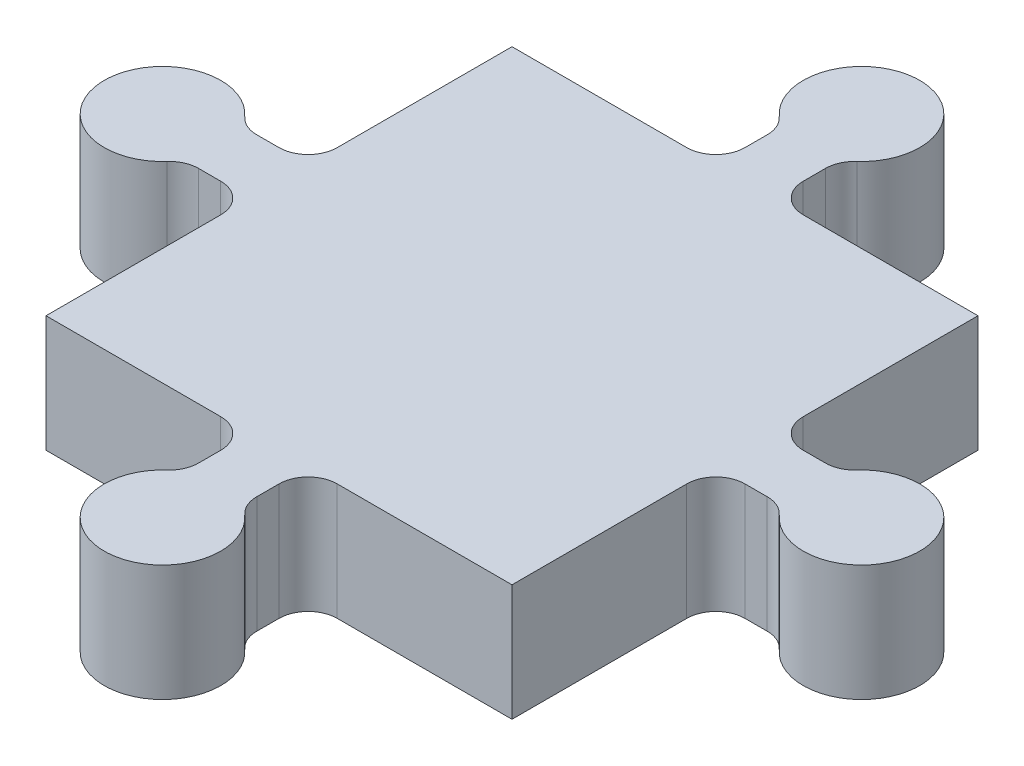
SolidWorks part; units mm, degrees
ref_plane "Front Plane" through (0, 0, 0) normal (0, 0, 1) x (1, 0, 0)
ref_plane "Top Plane" through (0, 0, 0) normal (0, 1, 0) x (1, 0, 0)
ref_plane "Right Plane" through (0, 0, 0) normal (1, 0, 0) x (0, 0, -1)
sketch "Sketch1" plane through (0, 0, 0) normal (0, 1, 0) x (1, 0, 0)
  line L0 (-4, 4) -> (4, -4) construction
  line L1 (-4, 4) -> (4, 4)
  line L2 (-4, 4) -> (-4, -4)
  line L3 (-4, -4) -> (4, -4)
  line L4 (4, 4) -> (4, -4)
  line L5 (-4, -4) -> (4, 4) construction
  line L6 (0, 6) -> (0, 4)
  line L7 (4, 0.5) -> (6, 0.5)
  line L8 (-0.5, 4) -> (0.5, 4)
  line L9 (-0.5, 4) -> (-0.5, 6)
  line L10 (-0.5, 6) -> (0.5, 6)
  line L11 (0.5, 4) -> (0.5, 6)
  line L12 (4, 0.5) -> (4, -0.5)
  line L13 (4, -0.5) -> (6, -0.5)
  line L14 (6, 0.5) -> (6, -0.5)
  line L15 (0.5, -4) -> (0.5, -6)
  line L16 (0.5, -4) -> (-0.5, -4)
  line L17 (-0.5, -4) -> (-0.5, -6)
  line L18 (0.5, -6) -> (-0.5, -6)
  line L19 (-4, -0.5) -> (-6, -0.5)
  line L20 (-4, -0.5) -> (-4, 0.5)
  line L21 (-4, 0.5) -> (-6, 0.5)
  line L22 (-6, -0.5) -> (-6, 0.5)
  circle A0 centre (0, 6) radius 1
  circle A1 centre (6, 0) radius 1
  circle A2 centre (0, -6) radius 1
  circle A3 centre (-6, 0) radius 1
  point P4 (0, 0)
  point P14 (0, 6)
  point P35 (0, 0)
  dimension "D3" = 2
  dimension "D1" = 8
  dimension "D2" = 8
  dimension "D4" = 2
  dimension "D5" = 1
  dimension "D6" = 4
extrude "Boss-Extrude1" add sketch "Sketch1" along normal blind 2 contours L4 L1 L2 L3 | L21 A3 L19 L22 | A3 L19 L2 L21 | A0 L6 L1 L11 | A0 L9 L1 L6 | L19 A3 L21 L22 | L9 A0 L6 L10 | L6 A0 L11 L10 | L11 A0 L9 L10 | L7 A1 L13 L14 | L13 A1 L7 L14 | L17 A2 L15 L18 | A2 L15 L3 L17 | L15 A2 L17 L18 | A1 L7 L4 L13
fillet "Fillet2" radius 0.5 16 edges at (0.5, 1, -4) (4, 1, -0.5) (5.134, 1, -0.5) (5.134, 1, 0.5) (4, 1, 0.5) (0.5, 1, 4) (0.5, 1, 5.134) (-0.5, 1, 5.134) (-0.5, 1, 4) (-4, 1, 0.5) (-5.134, 1, 0.5) (-5.134, 1, -0.5) (-4, 1, -0.5) (-0.5, 1, -4) (-0.5, 1, -5.134) (0.5, 1, -5.134)
equation "\"length\"= 8"
equation "\"D1@Sketch1\"= \"length\""
equation "\"D2@Sketch1\"= \"length\""
